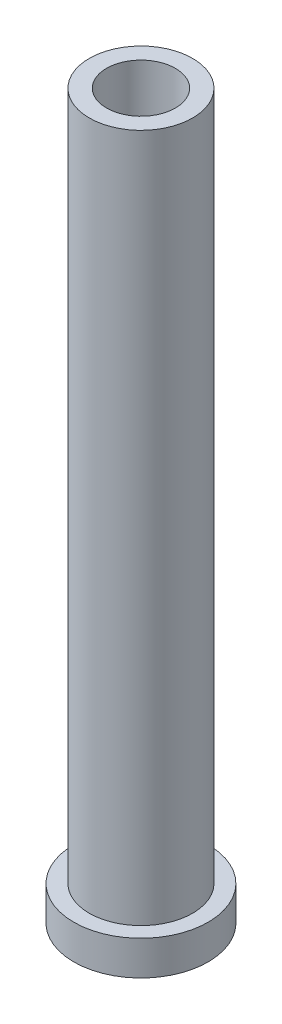
SolidWorks part; units mm, degrees
ref_plane "Front Plane" through (0, 0, 0) normal (0, 0, 1) x (1, 0, 0)
ref_plane "Top Plane" through (0, 0, 0) normal (0, 1, 0) x (1, 0, 0)
ref_plane "Right Plane" through (0, 0, 0) normal (1, 0, 0) x (0, 0, -1)
sketch "Sketch1" plane through (0, 0, 0) normal (0, 1, 0) x (1, 0, 0)
  circle A0 centre (0, 0) radius 3.9
  dimension "D1" = 7.8
extrude "Boss-Extrude1" add sketch "Sketch1" against normal blind 2
sketch "Sketch2" plane through (0, 0, 0) normal (0, 1, 0) x (1, 0, 0)
  circle A0 centre (0, 0) radius 3
  dimension "D1" = 6
extrude "Boss-Extrude2" add sketch "Sketch2" along normal blind 40
sketch "Sketch3" plane through (0, 40, 0) normal (0, 1, 0) x (1, 0, 0)
  circle A0 centre (0, 0) radius 2
  dimension "D1" = 4
extrude "Cut-Extrude1" cut sketch "Sketch3" against normal blind 5
